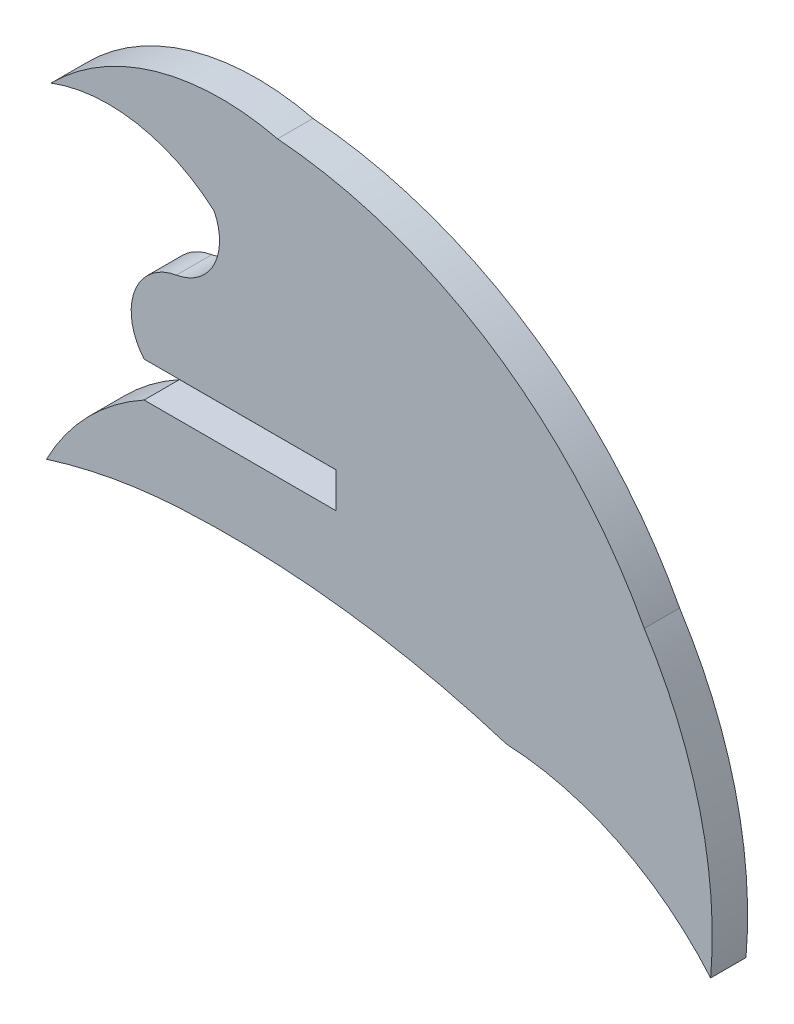
SolidWorks part; units mm, degrees
ref_plane "Front Plane" through (0, 0, 0) normal (0, 0, 1) x (1, 0, 0)
ref_plane "Top Plane" through (0, 0, 0) normal (0, 1, 0) x (1, 0, 0)
ref_plane "Right Plane" through (0, 0, 0) normal (1, 0, 0) x (0, 0, -1)
sketch "Sketch1" plane through (0, 0, 0) normal (0, 0, 1) x (1, 0, 0)
  line L0 (-10.9009, -3.6836) -> (-2.636, -3.681)
  line L1 (-2.636, -3.681) -> (-2.636, -2.1551)
  line L2 (-2.636, -2.1551) -> (-10.9017, -2.157)
  arc A0 (4.6971, -8.7125) -> (-9.2931, -6.9452) centre (-7.2161, -46.7615) ccw
  arc A2 (-9.5117, 1.6701) -> (-10.9017, -2.157) centre (-9.1139, -0.6403) ccw
  arc A3 (-9.5117, 1.6701) -> (-7.8858, 4.8806) centre (-9.8941, 3.8808) ccw
  arc A4 (-10.9009, -3.6836) -> (-15.106, -7.9956) centre (-5.9113, -12.7559) ccw
  arc A5 (10.6404, -1.4345) -> (-5.1525, 8.9324) centre (-6.6799, -10.6072) ccw
  arc A6 (-15.106, -7.9956) -> (-9.2931, -6.9452) centre (-8.075, -30.296) cw
  arc A7 (10.6404, -1.4345) -> (13.5003, -13.0431) centre (-4.9669, -11.4362) cw
  arc A8 (13.5003, -13.0431) -> (4.6971, -8.7125) centre (4.0988, -21.0416) ccw
  arc A9 (-7.8858, 4.8806) -> (-14.9074, 6.1326) centre (-12.4391, -0.34) ccw
  arc A10 (-14.9074, 6.1326) -> (-5.1525, 8.9324) centre (-7.5691, -1.0415) cw
extrude "Boss-Extrude1" add sketch "Sketch1" along normal blind 1.524
